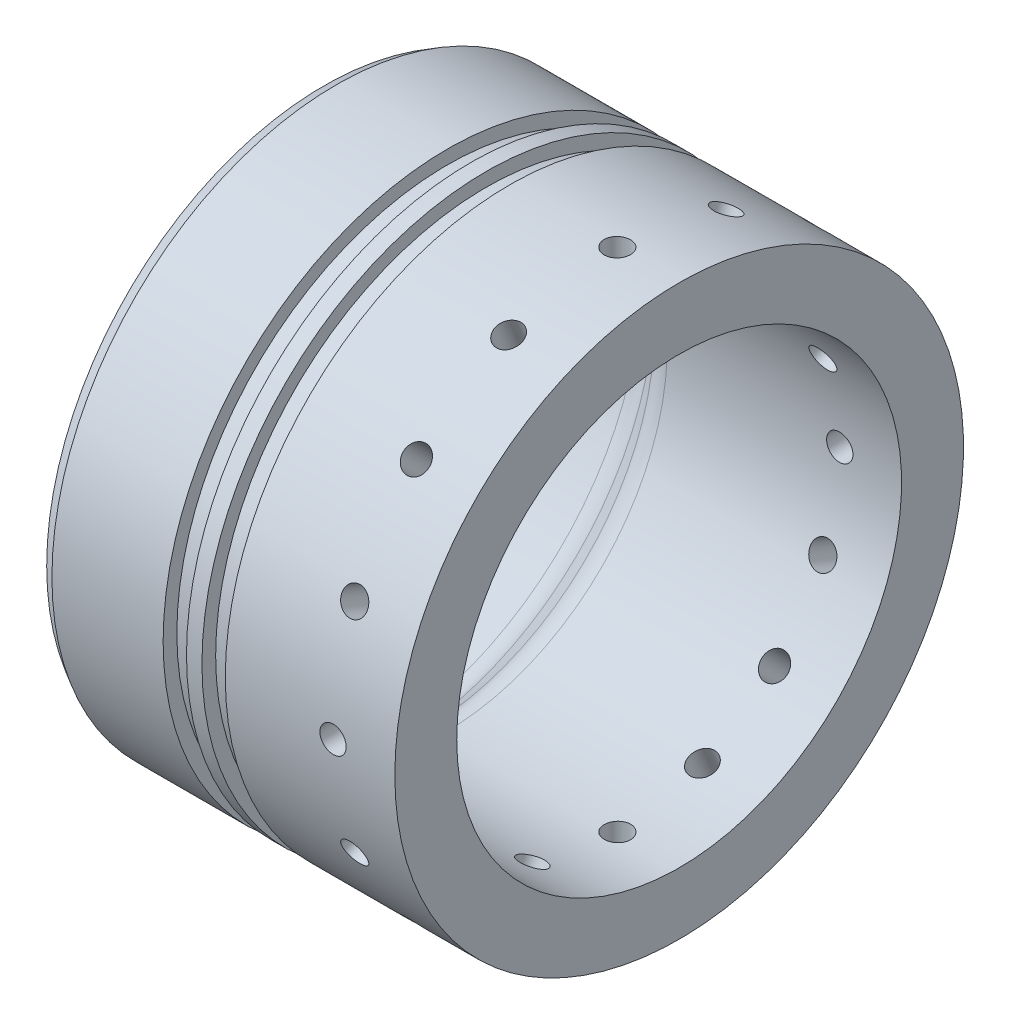
SolidWorks part; units mm, degrees
material "6061-T6 (SS)"
ref_plane "Front Plane" through (0, 0, 0) normal (0, 0, 1) x (1, 0, 0)
ref_plane "Top Plane" through (0, 0, 0) normal (0, 1, 0) x (1, 0, 0)
ref_plane "Right Plane" through (0, 0, 0) normal (1, 0, 0) x (0, 0, -1)
sketch "Sketch1" plane through (0, 0, 0) normal (0, 0, 1) x (1, 0, 0)
  line L2 (-18.5499, 3.2004) -> (-8.4802, 3.2004)
  line L12 (0, 58.4454) -> (98.3752, 58.4454) construction
  line L17 (-18.5499, 0) -> (6.8501, 0)
  line L18 (-18.5499, 3.2004) -> (-18.5499, 0)
  line L19 (-3.9901, 5.0603) -> (1.8152, 10.8655)
  line L20 (6.8501, 0) -> (6.8501, 2.8194)
  line L21 (6.8501, 2.8194) -> (11.6507, 2.8194)
  line L22 (11.6507, 2.8194) -> (11.6507, 0)
  line L23 (11.6507, 0) -> (14.8257, 0)
  line L24 (14.8257, 0) -> (14.8257, 2.8194)
  line L25 (14.8257, 2.8194) -> (19.6263, 2.8194)
  line L26 (19.6263, 2.8194) -> (19.6263, 0)
  line L27 (19.6263, 0) -> (54.4751, 0)
  line L28 (6.3053, 12.7254) -> (54.4751, 12.7254)
  line L29 (54.4751, 0) -> (54.4751, 12.7254)
  arc A0 (-3.9901, 5.0603) -> (-8.4802, 3.2004) centre (-8.4802, 9.5504) cw
  arc A1 (6.3053, 12.7254) -> (1.8152, 10.8655) centre (6.3053, 6.3754) ccw
  point P8 (-5.8499, 3.2004)
  point P22 (3.6751, 12.7254)
  dimension "D15" = 58.4454
  dimension "D8" = 6.35
  dimension "D9" = 6.35
  dimension "D2" = 12.7
  dimension "D3" = 55.245
  dimension "D4" = 9.525
  dimension "D5" = 45
  dimension "D6" = 25.4
  dimension "D7" = 50.8
  dimension "D10" = 4.8006
  dimension "D11" = 4.8006
  dimension "D12" = 3.175
  dimension "D13" = 2.8194
  dimension "D14" = 2.8194
revolve "Revolve1" add sketch "Sketch1" angle 360 about L12
ref_plane "Tap Reference Plane" through (0, 0, -58.4454) normal (0, 0, -1) x (-1, 0, 0)
sketch "Tap Reference" plane through (0, 0, -58.4454) normal (0, 0, -1) x (-1, 0, 0)
  line L0 (-54.4751, 58.4454) -> (-41.7751, 58.4454)
  line L1 (-54.4751, 116.8908) -> (-54.4751, 0) construction
  point P5 (-41.7751, 58.4454)
hole_wizard "Tap Drill for 1/4-28 Tap1" positions "Sketch4" profile "Sketch6" hole size "1/4-28" standard "ANSI Inch" end condition through all
sketch "Sketch4" plane through (0, 0, -58.4454) normal (0, 0, -1) x (-1, 0, 0)
  point P0 (-41.7751, 58.4454)
sketch "Sketch6" plane through (41.7751, 58.4454, -58.4454) normal (1, 0, 0) x (0, 1, 0)
  line L0 (0, 0) -> (0, 116.8908)
  line L1 (0, 116.8908) -> (2.7051, 116.8908)
  line L2 (2.7051, 116.8908) -> (2.7051, 0)
  line L5 (2.7051, 0) -> (0, 0)
  line L11 (0, -6.35) -> (0, 107.95) construction
  dimension "Thru Hole Dia." = 5.4102
  dimension "Thru Hole Depth" = 116.8908
pattern_circular "Tap Pattern" count 16 over 360 about axis through (0, 58.4454, 0) along (1, 0, 0) of "Tap Drill for 1/4-28 Tap1"
chamfer "Chamfer1" distance 2.54 angle 30 1 edges at (-18.5499, 58.4454, 58.4454)
